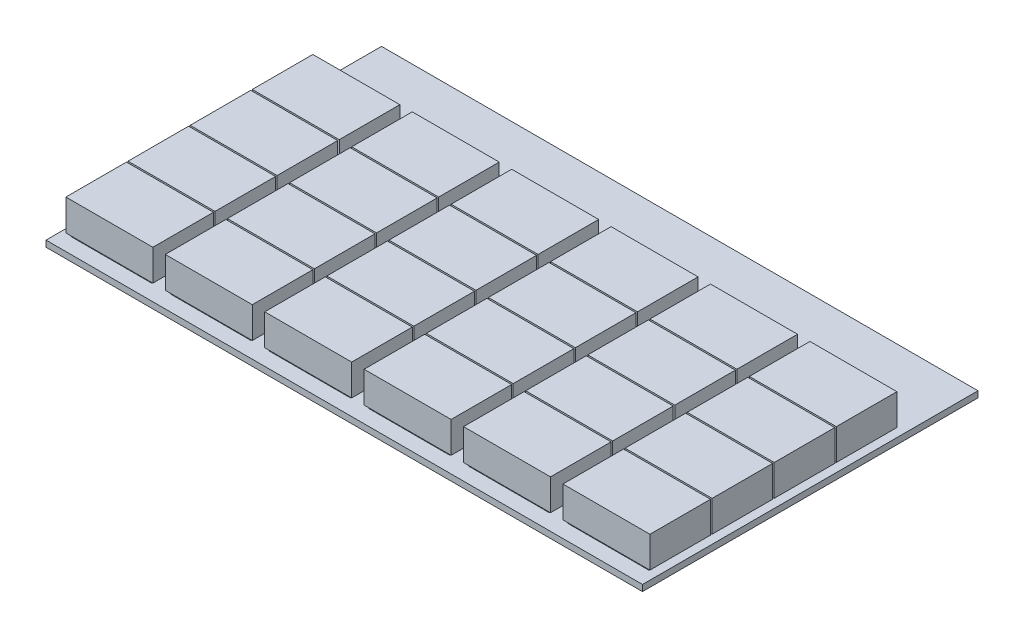
SolidWorks part; units mm, degrees
ref_plane "Front Plane" through (0, 0, 0) normal (0, 0, 1) x (1, 0, 0)
ref_plane "Top Plane" through (0, 0, 0) normal (0, 1, 0) x (1, 0, 0)
ref_plane "Right Plane" through (0, 0, 0) normal (1, 0, 0) x (0, 0, -1)
sketch "Sketch1" plane through (0, 0, 0) normal (0, 1, 0) x (1, 0, 0)
  line L1 (-40, -135) -> (40, -135)
  line L2 (-40, -135) -> (-40, 135)
  line L3 (-40, 135) -> (40, 135)
  line L4 (40, -135) -> (40, 135)
  line L5 (-40, -135) -> (40, 135) construction
  line L6 (-40, 135) -> (40, -135) construction
  point P0 (0, 0)
  dimension "D1" = 80
  dimension "D2" = 270
extrude "Boss-Extrude1" add sketch "Sketch1" along normal blind 5
sketch "Sketch2" plane through (0, 5, 0) normal (0, 1, 0) x (1, 0, 0)
  line L0 (0, 0) -> (0, -135) construction
  line L1 (-40, -135) -> (40, -135) construction
  line L3 (-32.5, -77.5) -> (32.5, -77.5)
  line L4 (-32.5, -77.5) -> (-32.5, -122.5)
  line L5 (-32.5, -122.5) -> (32.5, -122.5)
  line L6 (32.5, -77.5) -> (32.5, -122.5)
  line L7 (-32.5, -77.5) -> (32.5, -122.5) construction
  line L8 (-32.5, -122.5) -> (32.5, -77.5) construction
  point P5 (0, -100)
  dimension "D1" = 65
  dimension "D2" = 45
  dimension "D3" = 12.5
extrude "Boss-Extrude3" add sketch "Sketch2" along normal blind 2
pattern_linear "LPattern1" count 4 spacing 50 along (0, 0, -1) of "Boss-Extrude3"
sketch "Sketch3" plane through (0, 7, 0) normal (0, 1, 0) x (1, 0, 0)
  line L0 (0, 0) -> (0, -122.5) construction
  line L1 (-32.5, -122.5) -> (32.5, -122.5) construction
  line L2 (-40, 135) -> (-40, -135) construction
  line L3 (-35, -75.2605) -> (35, -75.2605)
  line L4 (-35, -75.2605) -> (-35, -124.0095)
  line L5 (-35, -124.0095) -> (35, -124.0095)
  line L6 (35, -75.2605) -> (35, -124.0095)
  line L7 (-35, -75.2605) -> (35, -124.0095) construction
  line L8 (-35, -124.0095) -> (35, -75.2605) construction
  point P5 (0, -99.635)
  dimension "D1" = 5
extrude "Boss-Extrude8" add sketch "Sketch3" along normal blind 25
pattern_linear "LPattern5" count 4 spacing 50 along (0, 0, -1) of "Boss-Extrude8"
pattern_linear "LPattern6" count 6 spacing 80 along (-1, 0, 0) of "Boss-Extrude1", "Boss-Extrude3", "LPattern1", "Boss-Extrude8", "LPattern5"
